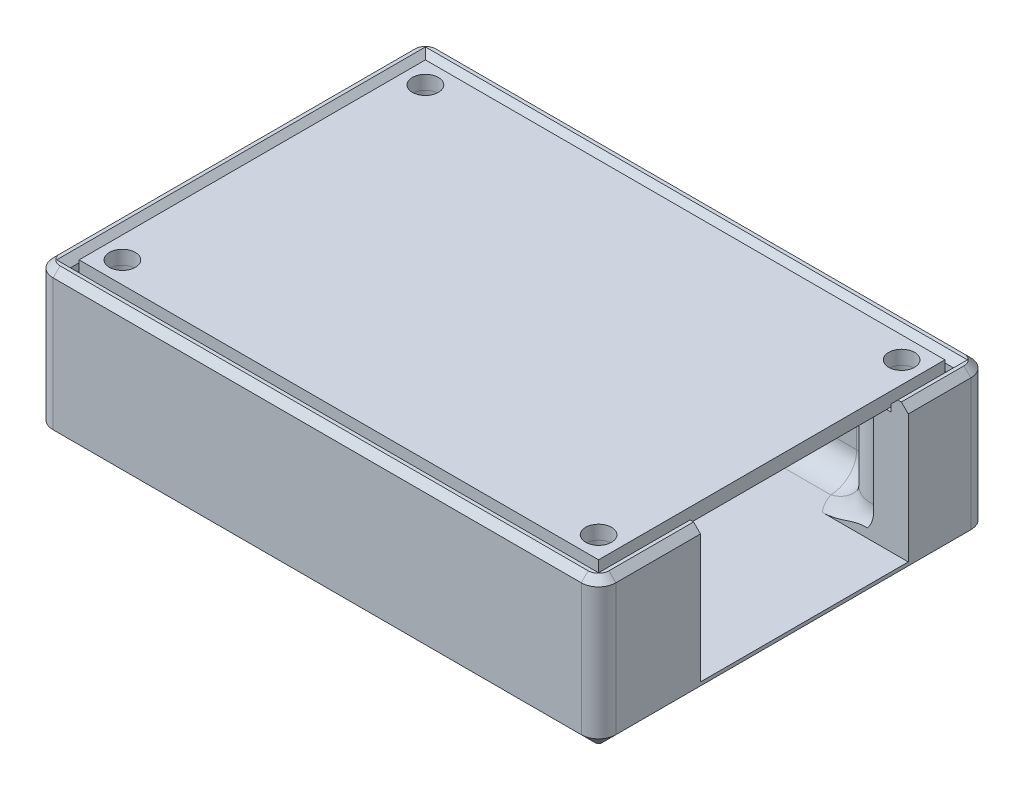
SolidWorks part; units mm, degrees
other "box"
other "PCB"
ref_plane "Front Plane" through (0, 0, 0) normal (0, 0, 1) x (1, 0, 0)
ref_plane "Top Plane" through (0, 0, 0) normal (0, 1, 0) x (1, 0, 0)
ref_plane "Right Plane" through (0, 0, 0) normal (1, 0, 0) x (0, 0, -1)
sketch "Sketch1" plane through (0, 0, 0) normal (0, 1, 0) x (1, 0, 0)
  line L1 (-30, -20) -> (30, -20)
  line L2 (-30, -20) -> (-30, 20)
  line L3 (-30, 20) -> (30, 20)
  line L4 (30, -20) -> (30, 20)
  line L5 (0, 20) -> (0, -20) construction
  line L6 (-30, 0) -> (30, 0) construction
  line L7 (27.5, -17.5) -> (-27.5, -17.5) construction
  line L8 (27.5, -17.5) -> (27.5, 17.5) construction
  line L9 (27.5, 17.5) -> (-27.5, 17.5) construction
  line L10 (-27.5, -17.5) -> (-27.5, 17.5) construction
  line L11 (0, 17.5) -> (0, -17.5) construction
  line L12 (27.5, 0) -> (-27.5, 0) construction
  circle A0 centre (27.5, 17.5) radius 2.5 construction
  circle A1 centre (27.5, 17.5) radius 1.5
  circle A2 centre (-27.5, 17.5) radius 1.5
  circle A3 centre (-27.5, -17.5) radius 1.5
  circle A4 centre (27.5, -17.5) radius 1.5
  point P0 (0, 0)
  point P4 (0, 0)
  point P13 (0, 0)
  dimension "D4" = 3
  dimension "D1" = 60
  dimension "D2" = 40
  dimension "D3" = 55
extrude "Boss-Extrude1" add sketch "Sketch1" along normal blind 1.6
sketch "Sketch2" plane through (0, 0, 0) normal (0, -1, 0) x (1, 0, 0)
  line L4 (32.5, -22.5) -> (32.5, 22.5)
  line L5 (32.5, 22.5) -> (-32.5, 22.5)
  line L6 (-32.5, 22.5) -> (-32.5, -22.5)
  line L7 (-32.5, -22.5) -> (32.5, -22.5)
  line L8 (30.5, -20.5) -> (30.5, 20.5)
  line L9 (-30.5, -20.5) -> (30.5, -20.5)
  line L10 (-30.5, 20.5) -> (-30.5, -20.5)
  line L11 (30.5, 20.5) -> (-30.5, 20.5)
  line L12 (30.5, -20.5) -> (30.5, 20.5) construction
  line L13 (-30.5, -20.5) -> (30.5, -20.5) construction
  line L14 (-30.5, 20.5) -> (-30.5, -20.5) construction
  line L15 (30.5, 20.5) -> (-30.5, 20.5) construction
  line L20 (-24.1459, 18.5) -> (24.1459, 18.5)
  line L21 (28.5, 14.1459) -> (28.5, -14.1459)
  line L22 (24.1459, -18.5) -> (-24.1459, -18.5)
  line L23 (-30.5, -15.6972) -> (-30.5, 15.6972)
  line L24 (28.5, -18.5) -> (28.5, 18.5)
  line L25 (-28.5, -18.5) -> (28.5, -18.5)
  line L26 (-28.5, 18.5) -> (-28.5, -18.5)
  line L27 (28.5, 18.5) -> (-28.5, 18.5)
  line L28 (28.5, -18.5) -> (28.5, 18.5) construction
  line L29 (-28.5, -18.5) -> (28.5, -18.5) construction
  line L30 (-28.5, 18.5) -> (-28.5, -18.5) construction
  line L31 (28.5, 18.5) -> (-28.5, 18.5) construction
  arc A0 (-24.1459, 18.5) -> (-30.5, 15.6972) centre (-27.5, 17.5) cw
  arc A1 (24.1459, 18.5) -> (28.5, 14.1459) centre (27.5, 17.5) ccw
  arc A2 (28.5, -14.1459) -> (24.1459, -18.5) centre (27.5, -17.5) ccw
  arc A3 (-30.5, -15.6972) -> (-24.1459, -18.5) centre (-27.5, -17.5) cw
  circle A4 centre (-27.5, 17.5) radius 1.5 construction
  circle A5 centre (-27.5, -17.5) radius 1.5 construction
  circle A6 centre (27.5, -17.5) radius 1.5 construction
  circle A7 centre (27.5, 17.5) radius 1.5 construction
  circle A8 centre (-27.5, 17.5) radius 1.5
  circle A9 centre (27.5, 17.5) radius 1.5
  circle A10 centre (27.5, -17.5) radius 1.5
  circle A11 centre (-27.5, -17.5) radius 1.5
  point P36 (-29.3895, -14.5539)
  point P37 (0, 0)
  dimension "D4" = 2
  dimension "D1" = 0.5
  dimension "D2" = 2
  dimension "D3" = 1.5
extrude "Boss-Extrude2" add sketch "Sketch2" along normal blind 14 separate body
sketch "Sketch3" plane through (0, 0, 0) normal (0, 1, 0) x (1, 0, 0)
  line L0 (30.5, 20.5) -> (30.5, -20.5) construction
  line L1 (32.5, 22.5) -> (32.5, -22.5) construction
  line L2 (32.5, -22.5) -> (-32.5, -22.5) construction
  line L3 (30.5, -20.5) -> (-30.5, -20.5) construction
  line L4 (-32.5, -22.5) -> (-32.5, 22.5) construction
  line L5 (-30.5, -20.5) -> (-30.5, 20.5) construction
  line L6 (-32.5, 22.5) -> (32.5, 22.5) construction
  line L7 (-30.5, 20.5) -> (30.5, 20.5) construction
  line L8 (30.5, 20.5) -> (30.5, -20.5)
  line L9 (32.5, 22.5) -> (32.5, -22.5)
  line L10 (32.5, -22.5) -> (-32.5, -22.5)
  line L11 (30.5, -20.5) -> (-30.5, -20.5)
  line L12 (-32.5, -22.5) -> (-32.5, 22.5)
  line L13 (-30.5, -20.5) -> (-30.5, 20.5)
  line L14 (-32.5, 22.5) -> (32.5, 22.5)
  line L15 (-30.5, 20.5) -> (30.5, 20.5)
extrude "Boss-Extrude3" add sketch "Sketch3" along normal blind 1.6
sketch "Sketch4" plane through (0, -14, 0) normal (0, -1, 0) x (1, 0, 0)
  line L0 (32.5, -22.5) -> (32.5, 22.5) construction
  line L1 (32.5, 22.5) -> (-32.5, 22.5) construction
  line L2 (-32.5, 22.5) -> (-32.5, -22.5) construction
  line L3 (-32.5, -22.5) -> (32.5, -22.5) construction
  line L4 (32.5, -22.5) -> (32.5, 22.5)
  line L5 (32.5, 22.5) -> (-32.5, 22.5)
  line L6 (-32.5, 22.5) -> (-32.5, -22.5)
  line L7 (-32.5, -22.5) -> (32.5, -22.5)
extrude "Boss-Extrude4" add sketch "Sketch4" along normal blind 2
fillet "Fillet3" radius 2 4 edges at (32.5, -7.2, 22.5) (-32.5, -7.2, 22.5) (32.5, -7.2, -22.5) (-32.5, -7.2, -22.5)
fillet "Fillet1" radius 3 7 edges at (24.1459, -7, -18.5) (28.5, -7, 14.1459) (24.1459, -7, 18.5) (-24.1459, -7, 18.5) (-30.5, -7, 15.6972) (-30.5, -7, -15.6972) (-24.1459, -7, -18.5)
fillet "Fillet2" radius 3 15 edges at (28.5, -14, -1.4153) (27.9258, -14, 13.0804) (25.0251, -14, 15.0251) (23.0804, -14, 17.9258) (0, -14, 18.5) (-23.0804, -14, 17.9258) (-25.4408, -14, 14.6699) (-29.6213, -14, 13.1213) (-30.5, -14, 0) (-29.6213, -14, -13.1213) (-25.4408, -14, -14.6699) (-23.0804, -14, -17.9258) (25.8709, -14, -14.4022) (23.0804, -14, -17.9258) (0, -14, -18.5)
chamfer "Chamfer1" distance 1.6 angle 45 8 edges at (-32.5, -16, 0) (0, -16, 22.5) (32.5, -16, 0) (0, -16, -22.5) (31.9142, -16, -21.9142) (-31.9142, -16, -21.9142) (-31.9142, -16, 21.9142) (31.9142, -16, 21.9142)
chamfer "Chamfer2" distance 0.8 angle 45 12 edges at (0, 1.6, 22.5) (-32.5, 1.6, 0) (0, 1.6, -22.5) (32.5, 1.6, 0) (0, 1.6, -20.5) (-30.5, 1.6, 0) (0, 1.6, 20.5) (30.5, 1.6, 0) (-31.9142, 1.6, 21.9142) (-31.9142, 1.6, -21.9142) (31.9142, 1.6, -21.9142) (31.9142, 1.6, 21.9142)
sketch "Sketch5" plane through (0, 1.6, 0) normal (0, 1, 0) x (1, 0, 0)
  line L0 (-30, 0) -> (30, 0) construction
  line L1 (32.5, -10.73) -> (0, -10.73)
  line L2 (32.5, -10.73) -> (32.5, 13.27)
  line L3 (32.5, 13.27) -> (0, 13.27)
  line L4 (0, -10.73) -> (0, 13.27)
  line L5 (16.25, 13.27) -> (16.25, -10.73) construction
  line L6 (32.5, 1.27) -> (0, 1.27) construction
  line L7 (0, 20) -> (0, -20) construction
  line L8 (32.5, 22.5) -> (32.5, -22.5) construction
  point P0 (16.25, 1.27)
  dimension "D1" = 24
  dimension "D2" = 1.27
extrude "Cut-Extrude1" cut sketch "Sketch5" against normal up to surface (15.6 mm away) up to face at (-27.5, -14, -19)
